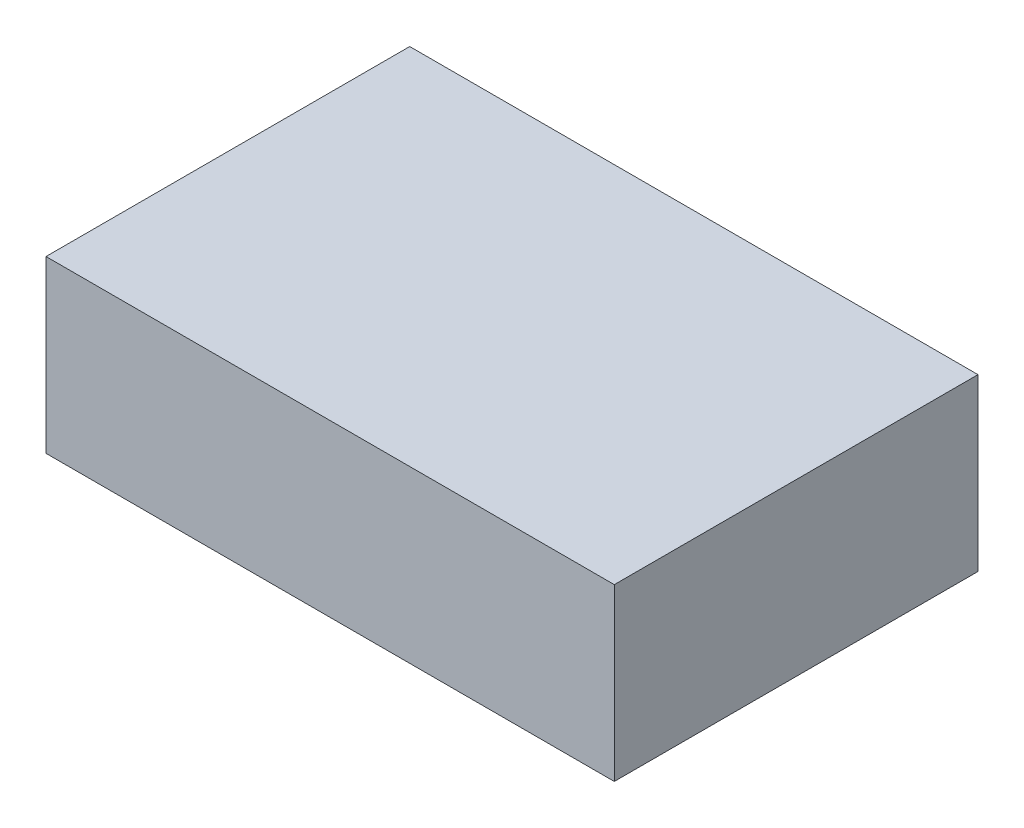
SolidWorks part; units mm, degrees
material "6061 合金"
ref_plane "前视基准面" through (0, 0, 0) normal (0, 0, 1) x (1, 0, 0)
ref_plane "上视基准面" through (0, 0, 0) normal (0, 1, 0) x (1, 0, 0)
ref_plane "右视基准面" through (0, 0, 0) normal (1, 0, 0) x (0, 0, -1)
sketch "草图1" plane through (0, 0, 0) normal (0, 1, 0) x (1, 0, 0)
  line L0 (0, 0) -> (50, 0)
  line L1 (50, 0) -> (50, 32)
  line L2 (50, 32) -> (0, 32)
  line L3 (0, 32) -> (0, 0)
extrude "凸台-拉伸1" add sketch "草图1" along normal blind 15
